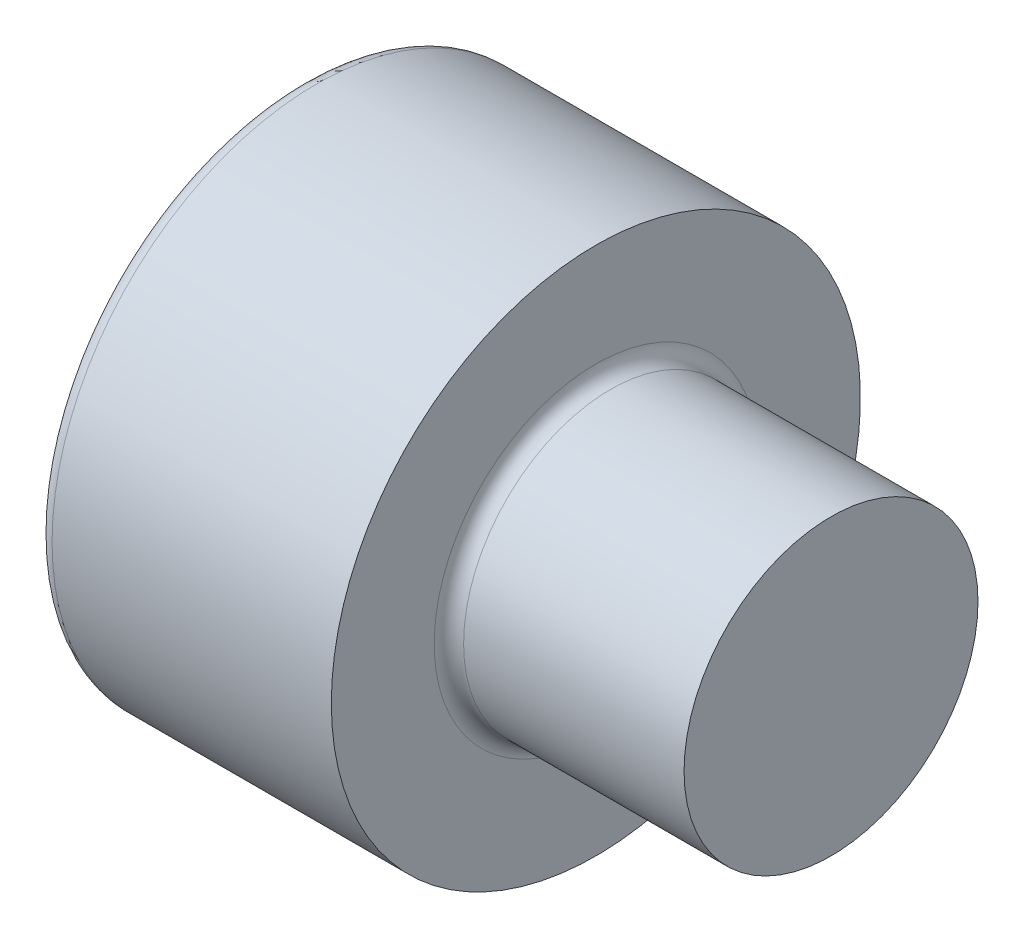
SolidWorks part; units mm, degrees
material "1023 Carbon Steel Sheet (SS)"
ref_plane "Front Plane" through (0, 0, 0) normal (0, 0, 1) x (1, 0, 0)
ref_plane "Top Plane" through (0, 0, 0) normal (0, 1, 0) x (1, 0, 0)
ref_plane "Right Plane" through (0, 0, 0) normal (1, 0, 0) x (0, 0, -1)
ref_plane "Plane1" through (0, 0, 0) normal (0, 0, -1) x (-1, 0, 0)
sketch "Sketch1" plane through (0, 0, 0) normal (0, 0, -1) x (-1, 0, 0)
  line L0 (-2.5, 2.25) -> (-2.5, 0)
  line L1 (-2.5, 0) -> (0, 0)
  line L2 (0, 0) -> (0, 2.25)
  line L3 (0, 2.25) -> (-2.5, 2.25)
  line L4 (-2.5, 0) -> (0, 0) construction
revolve "Revolve1" add sketch "Sketch1" angle 360 about L4
sketch "Sketch2" plane through (2.5, 0, 0) normal (1, 0, 0) x (0, 0, -1)
  circle A0 centre (0, 0) radius 1.25
extrude "Boss-Extrude1" add sketch "Sketch2" along normal blind 8
sketch "Sketch3" plane through (0, 0, 0) normal (-1, 0, 0) x (0, 0, 1)
  line L0 (-1.0225, -0.5903) -> (0, -1.1807)
  line L1 (0, -1.1807) -> (1.0225, -0.5903)
  line L2 (1.0225, -0.5903) -> (1.0225, 0.5903)
  line L3 (1.0225, 0.5903) -> (0, 1.1807)
  line L4 (0, 1.1807) -> (-1.0225, 0.5903)
  line L5 (-1.0225, 0.5903) -> (-1.0225, -0.5903)
extrude "Cut-Extrude1" cut sketch "Sketch3" against normal blind 1.1
sketch "Sketch4" plane through (0, 0, 0) normal (0, 0, 1) x (1, 0, 0)
  line L0 (1.1, 1.0225) -> (1.1, 0)
  line L1 (1.1, 0) -> (1.6903, 0)
  line L2 (1.6903, 0) -> (1.1, 1.0225)
  line L3 (1.1, 0) -> (1.6904, 0) construction
revolve "Cut-Revolve1" cut sketch "Sketch4" angle 360 about L3
chamfer "Chamfer1" distance 0.2535 angle 45 1 edges at (10.5, 0, -1.25)
fillet "Fillet1" radius 0.125 2 edges at (2.5, 0, -1.25) (0, 0, 2.25)
sketch "Sketch5" plane through (0, 0, 0) normal (0, 0, 1) x (1, 0, 0)
  line L0 (10.5, -0.9965) -> (10.5, 0.9965) construction
  line L1 (10.5, -2.709) -> (4.5, -2.709)
  line L2 (10.5, -2.709) -> (10.5, 1.9008)
  line L3 (10.5, 1.9008) -> (4.5, 1.9008)
  line L4 (4.5, -2.709) -> (4.5, 1.9008)
  dimension "D1" = 6
extrude "Cut-Extrude2" cut sketch "Sketch5" against normal blind 10 and the other way blind 10
